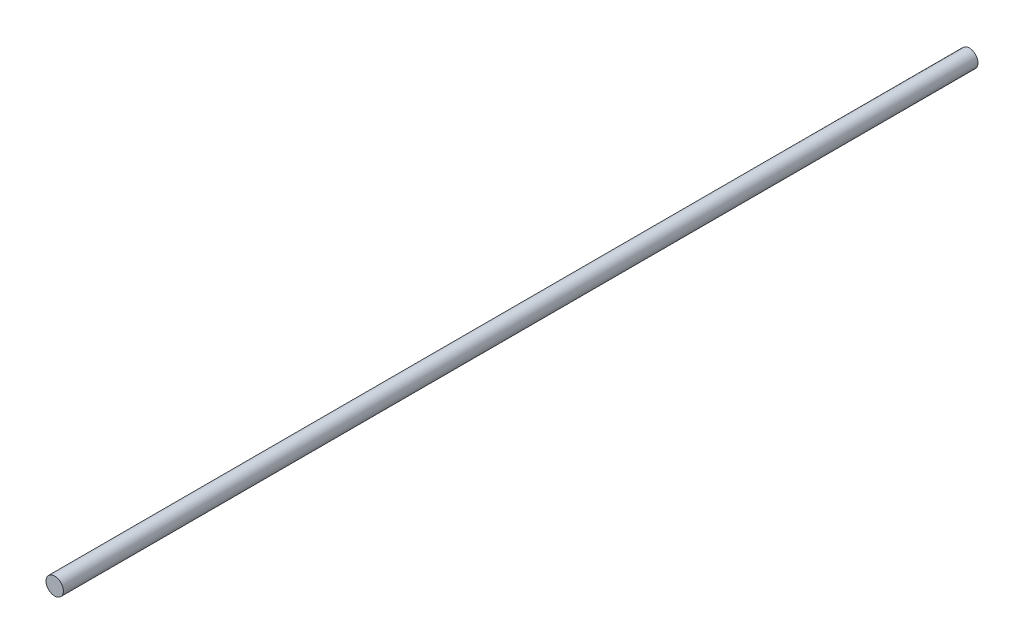
SolidWorks part; units mm, degrees
material "Acier inoxydable chromé"
ref_plane "Plan de face" through (0, 0, 0) normal (0, 0, 1) x (1, 0, 0)
ref_plane "Plan de dessus" through (0, 0, 0) normal (0, 1, 0) x (1, 0, 0)
ref_plane "Plan de droite" through (0, 0, 0) normal (1, 0, 0) x (0, 0, -1)
sketch "Esquisse1" plane through (0, 0, 0) normal (0, 0, 1) x (1, 0, 0)
  circle A0 centre (0, 0) radius 1.9
  dimension "D1" = 3.8
extrude "Boss.-Extru.1" add sketch "Esquisse1" along normal blind 200
